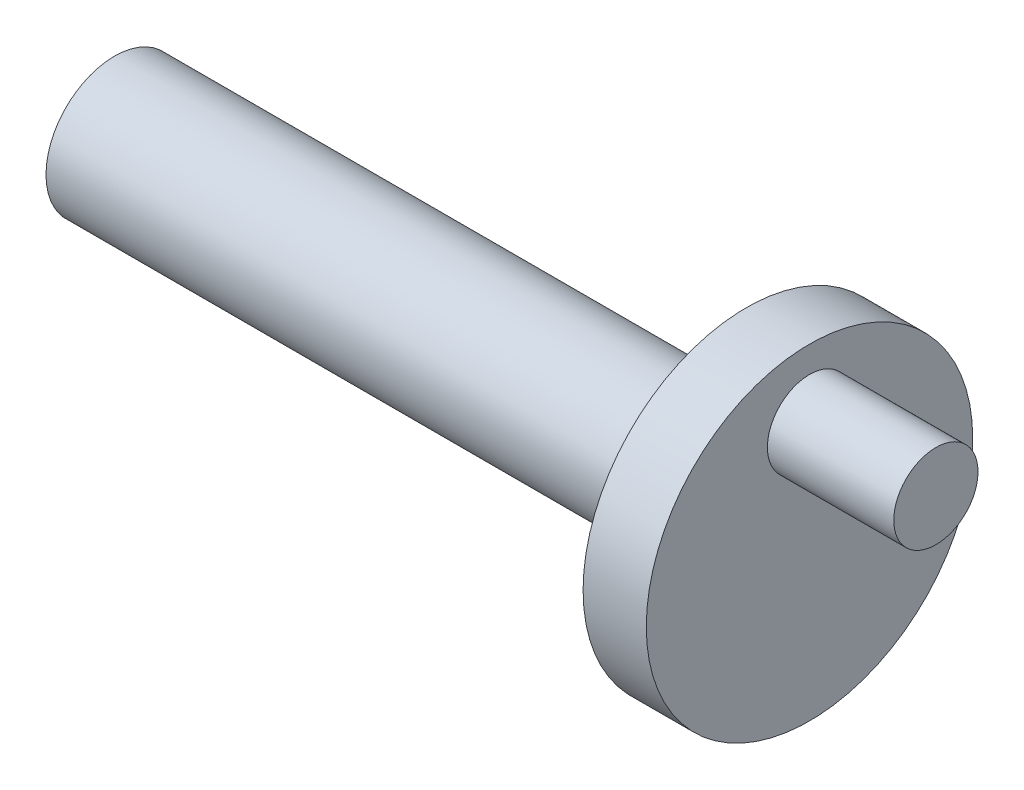
SolidWorks part; units mm, degrees
ref_plane "Front Plane" through (0, 0, 0) normal (0, 0, 1) x (1, 0, 0)
ref_plane "Top Plane" through (0, 0, 0) normal (0, 1, 0) x (1, 0, 0)
ref_plane "Right Plane" through (0, 0, 0) normal (1, 0, 0) x (0, 0, -1)
sketch "Sketch1" plane through (0, 0, 0) normal (1, 0, 0) x (0, 0, -1)
  circle A0 centre (0, 0) radius 15.5
  dimension "D1" = 31
extrude "Boss-Extrude1" add sketch "Sketch1" along normal blind 6
sketch "Sketch2" plane through (0, 0, 0) normal (-1, 0, 0) x (0, 0, 1)
  circle A0 centre (0, -0.3216) radius 6.5
  dimension "D1" = 13
extrude "Boss-Extrude2" add sketch "Sketch2" along normal blind 60
fillet "Fillet1" radius 1 1 edges at (0, -0.3216, 6.5)
sketch "Sketch3" plane through (6, 0, 0) normal (1, 0, 0) x (0, 0, -1)
  line L0 (0, 0) -> (0, 14.1639) construction
  circle A0 centre (0, 9) radius 4
  dimension "D1" = 8
  dimension "D2" = 9
extrude "Boss-Extrude3" add sketch "Sketch3" along normal blind 12
